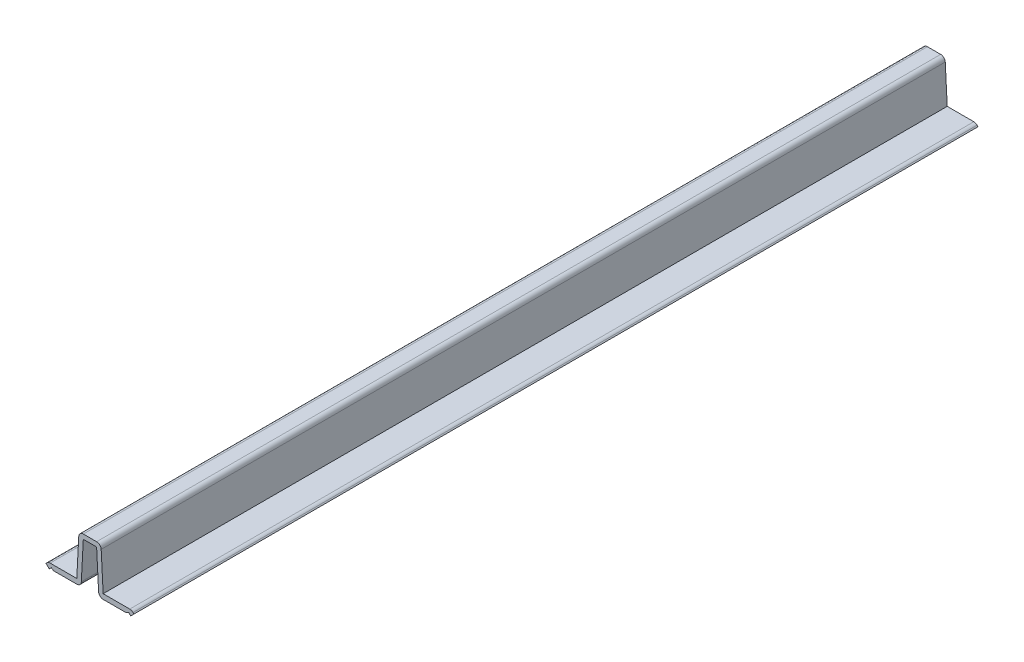
SolidWorks part; units mm, degrees
ref_plane "Front Plane" through (0, 0, 0) normal (0, 0, 1) x (1, 0, 0)
ref_plane "Top Plane" through (0, 0, 0) normal (0, 1, 0) x (1, 0, 0)
ref_plane "Right Plane" through (0, 0, 0) normal (1, 0, 0) x (0, 0, -1)
sketch "Sketch1" plane through (0, 0, 0) normal (0, 0, 1) x (1, 0, 0)
  line L0 (0, 0) -> (0, 17.0656) construction
  line L1 (0, 0) -> (-15.875, 0) construction
  line L2 (-4.7625, 1.9844) -> (-15.0601, 1.9844)
  line L3 (-15.0601, 1.9844) -> (-15.875, 1.1623)
  line L4 (-4.7625, 1.9844) -> (-3.9688, 17.0656)
  line L5 (-3.9688, 17.0656) -> (0, 17.0656)
  line L6 (-3.9911, 17.9978) -> (3.9464, 17.9978) construction
  line L7 (-15.875, 1.1623) -> (-14.7025, 0)
  line L8 (-14.7025, 0) -> (-13.9544, 0.7546)
  line L9 (-13.9544, 0.7546) -> (-13.1214, 0.1971)
  line L10 (-13.1214, 0.1971) -> (-3.2033, 0.1971)
  line L11 (-2.4024, 15.4146) -> (-3.2033, 0.1971)
  line L12 (2.4024, 15.4146) -> (0, 15.4146)
  line L13 (2.4024, 15.4146) -> (3.2033, 0.1971)
  line L14 (13.1214, 0.1971) -> (3.2033, 0.1971)
  line L15 (13.9544, 0.7546) -> (13.1214, 0.1971)
  line L16 (14.7025, 0) -> (13.9544, 0.7546)
  line L17 (15.875, 1.1623) -> (14.7025, 0)
  line L18 (-2.4024, 15.4146) -> (0, 15.4146)
  line L19 (15.0601, 1.9844) -> (15.875, 1.1623)
  line L20 (-13.1214, 0.1971) -> (-3.0887, 0.1971) construction
  line L21 (4.7625, 1.9844) -> (15.0601, 1.9844)
  line L22 (-3.1164, 1.8481) -> (-3.0887, 1.8481) construction
  line L23 (-3.1164, 1.8481) -> (-2.4024, 15.4146) construction
  line L24 (-3.1164, 1.8481) -> (-3.1164, 1.8481) construction
  line L25 (-3.1164, 1.8481) -> (-3.1164, 1.8481) construction
  line L26 (-3.1164, 1.8481) -> (-3.1164, 1.8481) construction
  line L27 (-3.1164, 1.8481) -> (-3.1164, 1.8481) construction
  line L28 (-3.1164, 1.8481) -> (-3.1164, 1.8481) construction
  line L29 (4.7625, 1.9844) -> (3.9688, 17.0656)
  line L30 (3.9688, 17.0656) -> (0, 17.0656)
  point P24 (0, 0)
  dimension "D1" = 1.651
  dimension "D2" = 31.75
  dimension "D3" = 31.75
  dimension "D4" = 1.651
  dimension "D5" = 9.525
  dimension "D6" = 7.9375
  dimension "D7" = 7.9375
  dimension "D8" = 15.0812
  dimension "D9" = 1.9844
  dimension "D10" = 1.7872
extrude "Boss-Extrude1" add sketch "Sketch1" against normal blind 304.8
fillet "Fillet1" radius 1.651 6 edges at (15.0601, 1.9844, -152.4) (-15.0601, 1.9844, -152.4) (-3.2033, 0.1971, -152.4) (3.2033, 0.1971, -152.4) (-3.9688, 17.0656, -152.4) (3.9688, 17.0656, -152.4)
